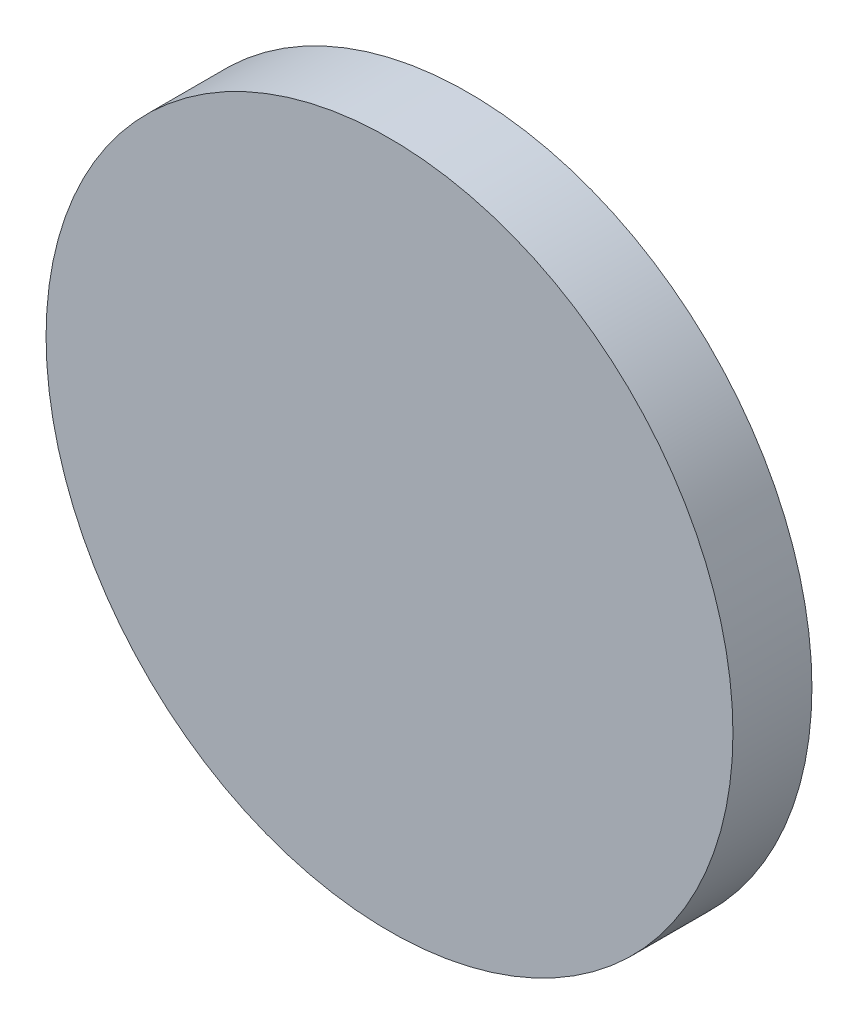
SolidWorks part; units mm, degrees
ref_plane "前视基准面" through (0, 0, 0) normal (0, 0, 1) x (1, 0, 0)
ref_plane "上视基准面" through (0, 0, 0) normal (0, 1, 0) x (1, 0, 0)
ref_plane "右视基准面" through (0, 0, 0) normal (1, 0, 0) x (0, 0, -1)
sketch "草图1" plane through (0, 0, 0) normal (0, 0, 1) x (1, 0, 0)
  circle A0 centre (72.41, 41.0422) radius 10
  dimension "D1" = 20
extrude "凸台-拉伸1" add sketch "草图1" along normal blind 2.3
